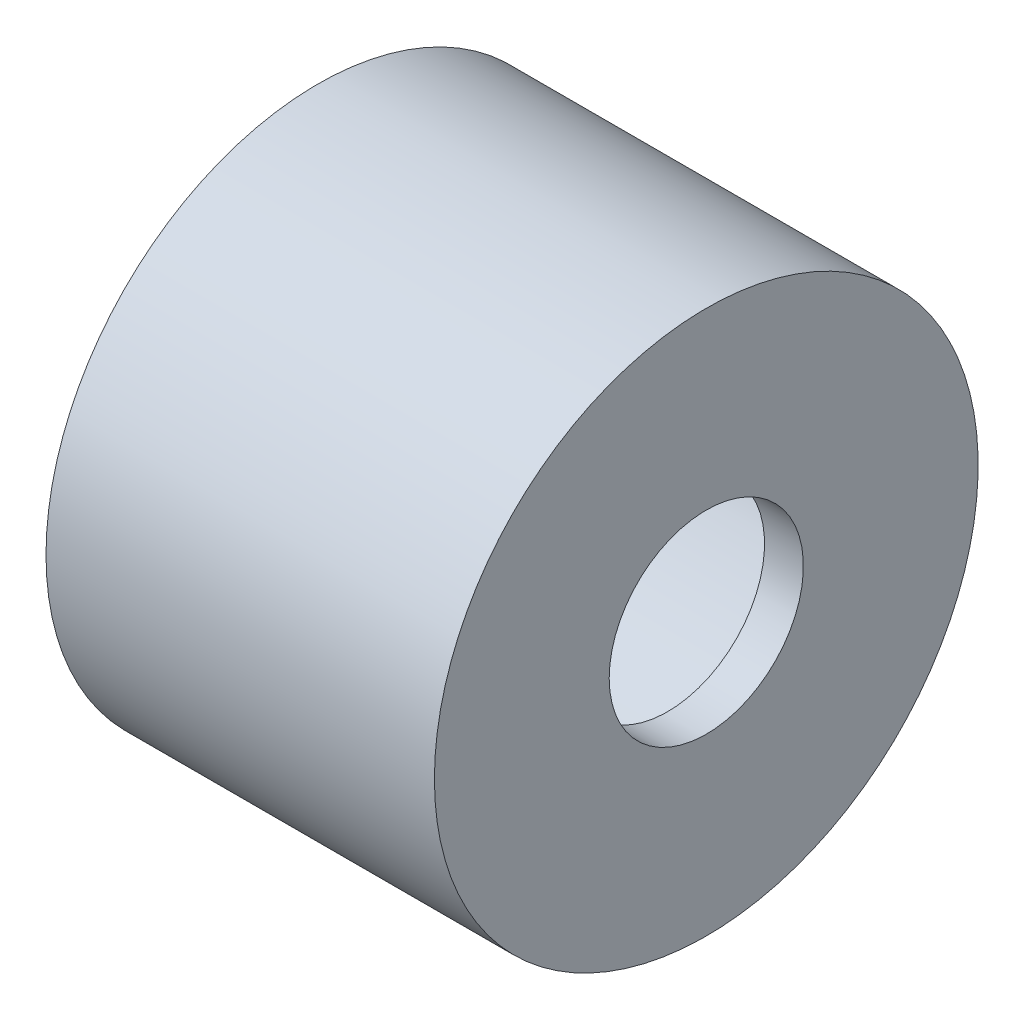
SolidWorks part; units mm, degrees
ref_plane "Front Plane" through (0, 0, 0) normal (0, 0, 1) x (1, 0, 0)
ref_plane "Top Plane" through (0, 0, 0) normal (0, 1, 0) x (1, 0, 0)
ref_plane "Right Plane" through (0, 0, 0) normal (1, 0, 0) x (0, 0, -1)
sketch "Sketch1" plane through (0, 0, 0) normal (0, 0, 1) x (1, 0, 0)
  line L0 (-0.3053, 0) -> (21740.3982, 0) construction
  line L1 (0, 7.62) -> (11.43, 7.62)
  line L2 (11.43, 7.62) -> (11.43, 3.175)
  line L3 (0, 8.89) -> (12.7, 8.89)
  line L4 (12.7, 8.89) -> (12.7, 3.175)
  line L5 (11.43, 3.175) -> (12.7, 3.175)
  line L6 (12.7, 8.89) -> (12.7, 2.8575) construction
  line L7 (11.43, 7.62) -> (11.43, 2.8575) construction
  line L8 (0, 8.89) -> (0, 7.62)
  dimension "D1" = 15.24
  dimension "D3" = 6.35
  dimension "D4" = 12.7
  dimension "D2" = 1.27
revolve "Revolve1" add sketch "Sketch1" angle 360 about L0
